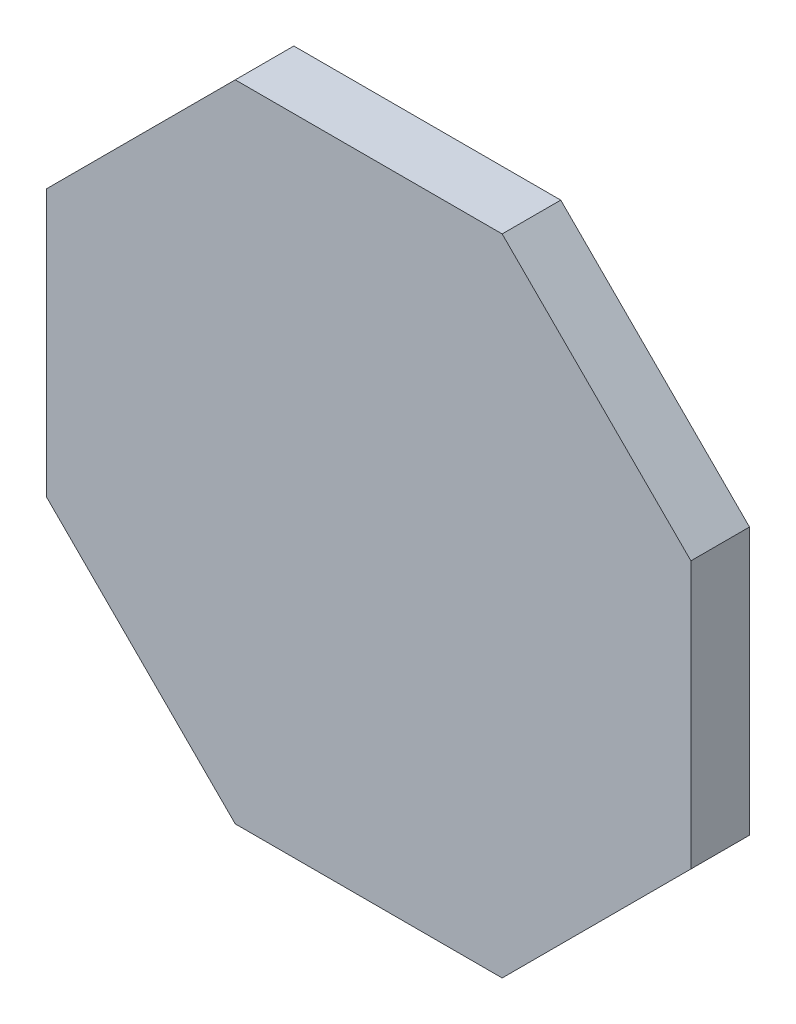
SolidWorks part; units mm, degrees
material "ABS PC"
ref_plane "Front Plane" through (0, 0, 0) normal (0, 0, 1) x (1, 0, 0)
ref_plane "Top Plane" through (0, 0, 0) normal (0, 1, 0) x (1, 0, 0)
ref_plane "Right Plane" through (0, 0, 0) normal (1, 0, 0) x (0, 0, -1)
sketch "Sketch1" plane through (0, 0, 0) normal (0, 0, 1) x (1, 0, 0)
  line L1 (55, 22.7817) -> (22.7817, 55)
  line L2 (22.7817, 55) -> (-22.7817, 55)
  line L3 (-22.7817, 55) -> (-55, 22.7817)
  line L4 (-55, 22.7817) -> (-55, -22.7817)
  line L5 (-55, -22.7817) -> (-22.7817, -55)
  line L6 (-22.7817, -55) -> (22.7817, -55)
  line L7 (22.7817, -55) -> (55, -22.7817)
  line L8 (55, -22.7817) -> (55, 22.7817)
  circle A0 centre (0, 0) radius 55 construction
extrude "Boss-Extrude1" add sketch "Sketch1" along normal blind 10
